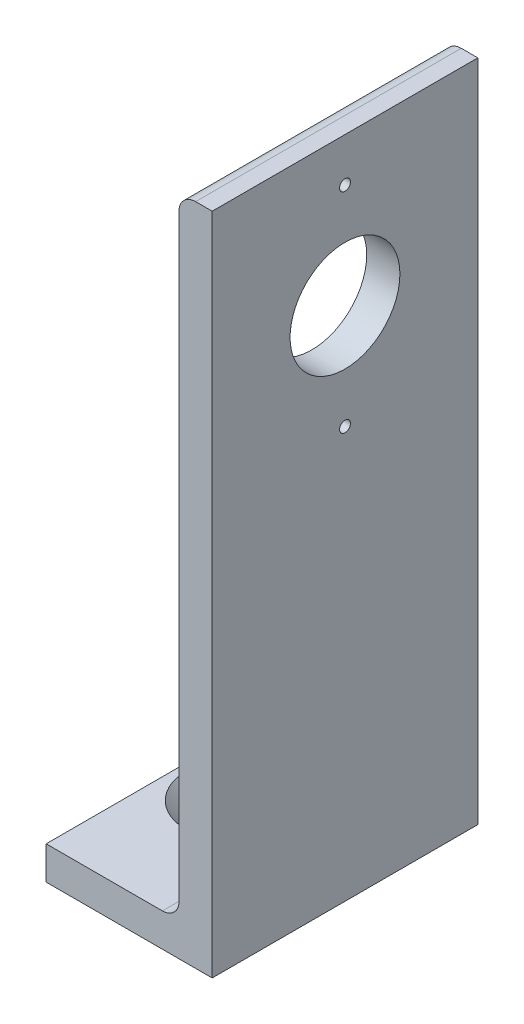
SolidWorks part; units mm, degrees
ref_plane "Front Plane" through (0, 0, 0) normal (0, 0, 1) x (1, 0, 0)
ref_plane "Top Plane" through (0, 0, 0) normal (0, 1, 0) x (1, 0, 0)
ref_plane "Right Plane" through (0, 0, 0) normal (1, 0, 0) x (0, 0, -1)
sketch "Sketch2" plane through (0, 0, 0) normal (0, 0, 1) x (1, 0, 0)
  line L0 (-15.875, 0) -> (15.875, 0)
  line L1 (15.875, 0) -> (15.875, 127)
  line L2 (15.875, 127) -> (9.525, 127) construction
  line L3 (9.525, 123.825) -> (9.525, 9.525)
  line L4 (6.35, 6.35) -> (-15.875, 6.35)
  line L5 (-15.875, 6.35) -> (-15.875, 0)
  line L6 (12.7, 127) -> (15.875, 127)
  arc A0 (9.525, 123.825) -> (12.7, 127) centre (12.7, 123.825) cw
  arc A2 (9.525, 9.525) -> (6.35, 6.35) centre (6.35, 9.525) cw
  dimension "Vert" = 127
  dimension "Horz" = 31.75
  dimension "Thickness" = 6.35
extrude "Boss-Extrude1" add sketch "Sketch2" along normal mid plane 50.8
ref_plane "Contact Plane 1" through (0, 6.35, 0) normal (0, 1, 0) x (1, 0, 0)
ref_plane "Contact Plane 2" through (9.525, 0, 0) normal (-1, 0, 0) x (0, 0, 1)
sketch "Sketch3" plane through (0, 0, 0) normal (0, -1, 0) x (1, 0, 0)
  line L0 (15.875, 0) -> (-15.875, 0)
  line L1 (15.875, 25.4) -> (15.875, -25.4) construction
  line L3 (-15.875, 25.4) -> (-15.875, -25.4) construction
  circle A0 centre (-4.826, 0) radius 4.765
  dimension "D1" = 9.53
  dimension "D2" = 20.701
extrude "Cut-Extrude1" cut sketch "Sketch3" against normal through all contours A0
sketch "Sketch4" plane through (15.875, 0, 0) normal (1, 0, 0) x (0, 0, -1)
  line L0 (-25.4, 0) -> (-25.4, 127) construction
  circle A1 centre (0, 98.65) radius 10.5
  dimension "D1" = 25.4
  dimension "D2" = 21
  dimension "D3" = 98.65
extrude "Cut-Extrude2" cut sketch "Sketch4" against normal blind 12.7
sketch "Sketch5" plane through (15.875, 0, 0) normal (1, 0, 0) x (0, 0, -1)
  line L0 (0, 98.65) -> (-32.3063, 98.65) construction
  circle A0 centre (0, 78.65) radius 1.04
  circle A1 centre (0, 118.65) radius 1.04
  dimension "D1" = 2.08
  dimension "D2" = 20
extrude "Cut-Extrude3" cut sketch "Sketch5" against normal blind 10
thread "Thread1" pitch 0.45 start angle 0, offset 0, length 0, pitch 0.45, diameter 2.08
ref_plane "Plane2" through (15.875, 118.65, 1.04) normal (0, -1, 0) x (0, 0, 1)
sketch "Thread Profile2" plane through (15.875, 118.65, 1.04) normal (0, -1, 0) x (0, 0, 1)
  line L0 (0, 0) -> (0, 0.45) construction
  line L11 (0, 0) -> (0, 0.3937)
  line L12 (0, 0.3937) -> (-0.2436, 0.2531)
  line L13 (-0.2436, 0.2531) -> (-0.2436, 0.1406)
  line L15 (-0.2436, 0.1406) -> (0, 0)
  line L17 (-0.2436, 0.1969) -> (0, 0.1969) construction
  point P2 (0, 0)
  dimension "Pitch" = 0.45
  dimension "Profile_Angle" = 60
  dimension "Profile_Land" = 0.1125
  dimension "Profile_Height" = 0.2436
thread "Thread2" pitch 0.45 start angle 0, offset 0, length 0, pitch 0.45, diameter 2.08
ref_plane "Plane3" through (15.875, 78.65, 1.04) normal (0, -1, 0) x (0, 0, 1)
sketch "Thread Profile3" plane through (15.875, 78.65, 1.04) normal (0, -1, 0) x (0, 0, 1)
  line L0 (0, 0) -> (0, 0.45) construction
  line L11 (0, 0) -> (0, 0.3937)
  line L12 (0, 0.3937) -> (-0.2436, 0.2531)
  line L13 (-0.2436, 0.2531) -> (-0.2436, 0.1406)
  line L15 (-0.2436, 0.1406) -> (0, 0)
  line L17 (-0.2436, 0.1969) -> (0, 0.1969) construction
  point P2 (0, 0)
  dimension "Pitch" = 0.45
  dimension "Profile_Angle" = 60
  dimension "Profile_Land" = 0.1125
  dimension "Profile_Height" = 0.2436
hole_wizard "CSK for 3/8 Flat Head Machine Screw1" positions "Sketch6" profile "Sketch7" countersink size "3/8" standard "ANSI Inch" end condition through all
sketch "Sketch6" plane through (0, 6.35, 0) normal (0, 1, 0) x (1, 0, 0)
  point P0 (-4.826, 0)
sketch "Sketch7" plane through (-4.826, 6.35, 0) normal (1, 0, 0) x (0, 0, 1)
  line L0 (0, 0) -> (0, 6.35)
  line L1 (0, 6.35) -> (5.1587, 6.35)
  line L2 (5.1587, 6.35) -> (5.1587, 5.1981)
  line L3 (5.1587, 5.1981) -> (9.6774, 0)
  line L5 (9.6774, 0) -> (0, 0)
  line L6 (-5.1587, 5.1981) -> (-9.6774, 0) construction
  line L11 (0, -6.35) -> (0, 107.95) construction
  dimension "Thru Hole Dia." = 10.3175
  dimension "Thru Hole Depth" = 6.35
  dimension "Near C'Sink Dia." = 19.3548
  dimension "Near C'Sink Angle" = 82
